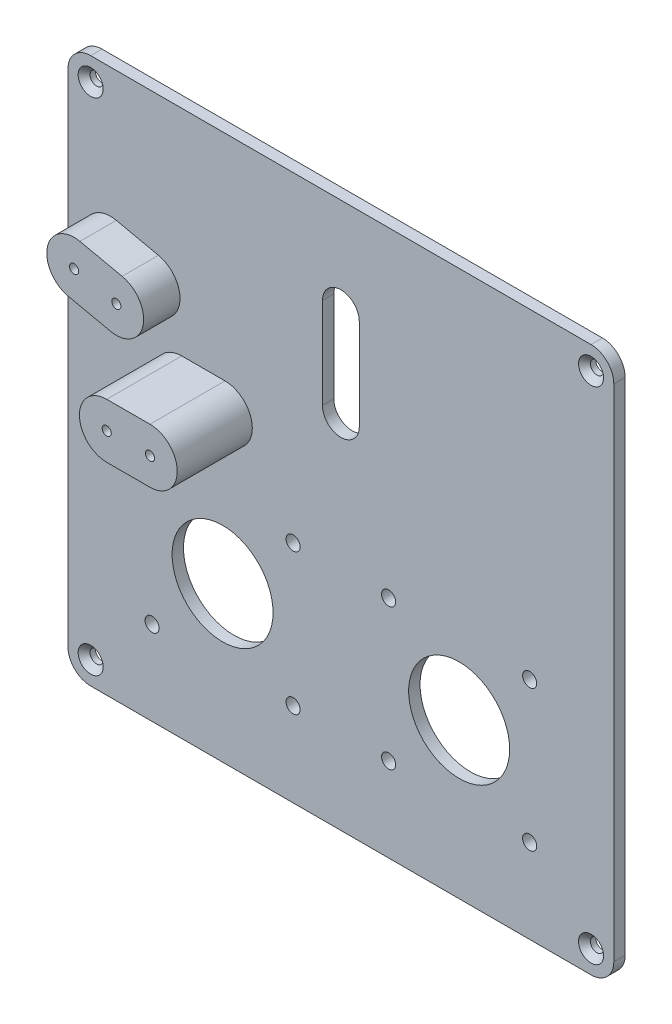
SolidWorks part; units mm, degrees
ref_plane "Front Plane" through (0, 0, 0) normal (0, 0, 1) x (1, 0, 0)
ref_plane "Top Plane" through (0, 0, 0) normal (0, 1, 0) x (1, 0, 0)
ref_plane "Right Plane" through (0, 0, 0) normal (1, 0, 0) x (0, 0, -1)
sketch "Sketch1" plane through (0, 0, 0) normal (0, 0, 1) x (1, 0, 0)
  line L1 (86, -34) -> (-34, -34)
  line L2 (86, -34) -> (86, 86)
  line L3 (86, 86) -> (-34, 86)
  line L4 (-34, -34) -> (-34, 86)
  line L6 (73, 0) -> (86, 0) construction
  line L7 (73, -17) -> (73, 17) construction
  line L8 (-21, 0) -> (-34, 0) construction
  line L9 (-21, 17) -> (-21, -17) construction
  line L10 (35, -21) -> (69, -21) construction
  line L11 (52, 0) -> (0, 0) construction
  line L12 (26, 0) -> (26, 54.8845) construction
  line L13 (53.4457, 56.6124) -> (56.9901, 0.3142)
  line L14 (7.2779, 34.7417) -> (48.596, -3.6623)
  circle A0 centre (0, 0) radius 11 construction
  circle A1 centre (52, 0) radius 11 construction
  circle A2 centre (0, 0) radius 11
  circle A3 centre (52, 0) radius 11
  circle A7 centre (36.5, 15.5) radius 1.5 construction
  circle A14 centre (-15.5, -15.5) radius 1.5 construction
  circle A15 centre (-15.5, 15.5) radius 1.5 construction
  circle A16 centre (15.5, 15.5) radius 1.5 construction
  circle A17 centre (15.5, -15.5) radius 1.5 construction
  circle A18 centre (36.5, -15.5) radius 1.5 construction
  circle A19 centre (67.5, 15.5) radius 1.5 construction
  circle A20 centre (67.5, -15.5) radius 1.5 construction
  circle A21 centre (-15.5, -15.5) radius 1.5
  circle A22 centre (-15.5, 15.5) radius 1.5
  circle A23 centre (15.5, 15.5) radius 1.5
  circle A24 centre (15.5, -15.5) radius 1.5
  circle A25 centre (36.5, 15.5) radius 1.5
  circle A26 centre (36.5, -15.5) radius 1.5
  circle A27 centre (67.5, 15.5) radius 1.5
  circle A28 centre (67.5, -15.5) radius 1.5
  arc A29 (53.4457, 56.6124) -> (7.2779, 34.7417) centre (26, 54.8845) ccw
  arc A30 (48.596, -3.6623) -> (56.9901, 0.3142) centre (52, 0) ccw
  circle A31 centre (0, 0) radius 5
  circle A32 centre (26, 54.8845) radius 4
  dimension "D4" = 27.5
  dimension "D5" = 10
  dimension "D6" = 232
  dimension "D7" = 8
  dimension "D1" = 120
  dimension "D2" = 120
  dimension "D3" = 13
sketch "Sketch4" plane through (0, 0, 0) normal (0, 0, 1) x (1, 0, 0)
  line L0 (26, 64.8845) -> (26, 44.8845) construction
  line L1 (26, 0) -> (26, 54.8845) construction
  line L2 (30.05, 64.8845) -> (30.05, 44.8845)
  line L3 (21.95, 64.8845) -> (21.95, 44.8845)
  line L4 (86, -34) -> (86, 86) construction
  line L5 (86, 86) -> (-34, 86) construction
  line L6 (-34, -34) -> (-34, 86) construction
  line L7 (86, -34) -> (-34, -34) construction
  line L8 (86, -34) -> (86, 86)
  line L9 (86, 86) -> (-34, 86)
  line L10 (-34, -34) -> (-34, 86)
  line L11 (86, -34) -> (-34, -34)
  arc A0 (30.05, 64.8845) -> (21.95, 64.8845) centre (26, 64.8845) ccw
  arc A1 (21.95, 44.8845) -> (30.05, 44.8845) centre (26, 44.8845) ccw
  point P5 (26, 54.8845)
  point P12 (67.5, -15.5)
  point P15 (36.5, -15.5)
  point P17 (36.5, 15.5)
  point P19 (67.5, 15.5)
  point P21 (15.5, 15.5)
  point P23 (-15.5, 15.5)
  point P25 (-15.5, -15.5)
  point P27 (15.5, -15.5)
  point P29 (52, 0)
  point P31 (0, 0)
  dimension "D2" = 4.05
  dimension "D1" = 20
extrude "Boss-Extrude2" add sketch "Sketch4" along normal blind 2.5
fillet "Fillet1" radius 5 4 edges at (86, 86, 1.25) (-34, 86, 1.25) (-34, -34, 1.25) (86, -34, 1.25)
sketch "Sketch5" plane through (0, 0, 0) normal (0, 0, -1) x (-1, 0, 0)
  line L4 (29, 86) -> (-81, 86)
  line L5 (-86, 81) -> (-86, -29)
  line L6 (-81, -34) -> (29, -34)
  line L7 (34, -29) -> (34, 81)
  line L8 (29, 86) -> (-81, 86)
  line L9 (-86, 81) -> (-86, -29)
  line L10 (-81, -34) -> (29, -34)
  line L11 (34, -29) -> (34, 81)
  arc A4 (-81, 86) -> (-86, 81) centre (-81, 81) ccw
  arc A5 (-86, -29) -> (-81, -34) centre (-81, -29) ccw
  arc A6 (29, -34) -> (34, -29) centre (29, -29) ccw
  arc A7 (34, 81) -> (29, 86) centre (29, 81) ccw
  arc A8 (-81, 86) -> (-86, 81) centre (-81, 81) ccw
  arc A9 (-86, -29) -> (-81, -34) centre (-81, -29) ccw
  arc A10 (29, -34) -> (34, -29) centre (29, -29) ccw
  arc A11 (34, 81) -> (29, 86) centre (29, 81) ccw
  dimension "D1" = 0
hole_wizard "Ø3.1 (3.1) Diameter Hole1" positions "Sketch6" profile "Sketch7" hole size "Ø3.1" standard "ANSI Metric" end condition through all
sketch "Sketch6" plane through (0, 0, 2.5) normal (0, 0, 1) x (1, 0, 0)
  point P0 (-15.5, -15.5)
  point P3 (-15.5, 15.5)
  point P6 (15.5, 15.5)
  point P9 (15.5, -15.5)
  point P12 (36.5, -15.5)
  point P15 (36.5, 15.5)
  point P18 (67.5, -15.5)
  point P21 (67.5, 15.5)
sketch "Sketch7" plane through (-15.5, -15.5, 2.5) normal (1, 0, 0) x (0, -1, 0)
  line L0 (0, 0) -> (0, 2.5)
  line L1 (0, 2.5) -> (1.55, 2.5)
  line L2 (1.55, 2.5) -> (1.55, 0)
  line L5 (1.55, 0) -> (0, 0)
  line L11 (0, -6.35) -> (0, 107.95) construction
  dimension "Thru Hole Dia." = 3.1
  dimension "Thru Hole Depth" = 2.5
sketch "Sketch8" plane through (0, 0, 2.5) normal (0, 0, 1) x (1, 0, 0)
  circle A5 centre (0, 0) radius 11.1
  circle A6 centre (0, 0) radius 11.1
  circle A8 centre (52, 0) radius 11.1
  circle A9 centre (52, 0) radius 11.1
  dimension "D1" = 0.1
  dimension "D2" = 0.1
extrude "Cut-Extrude1" cut sketch "Sketch8" against normal blind 10
sketch "Sketch9" plane through (0, 0, 2.5) normal (0, 0, 1) x (1, 0, 0)
  line L0 (26, 44.8845) -> (26, 64.8845) construction
  line L1 (21.9, 44.8845) -> (21.9, 64.8845)
  line L2 (30.1, 44.8845) -> (30.1, 64.8845)
  arc A0 (21.9, 44.8845) -> (30.1, 44.8845) centre (26, 44.8845) ccw
  arc A1 (30.1, 64.8845) -> (21.9, 64.8845) centre (26, 64.8845) ccw
  point P2 (26, 54.8845)
  dimension "D1" = 4.1
sketch "Sketch10" plane through (0, 0, 2.5) normal (0, 0, 1) x (1, 0, 0)
  line L0 (-8.9685, 32.85) -> (0.5315, 32.85) construction
  line L1 (-8.9685, 38.85) -> (0.5315, 38.85)
  line L2 (-8.9685, 26.85) -> (0.5315, 26.85)
  arc A0 (-8.9685, 38.85) -> (-8.9685, 26.85) centre (-8.9685, 32.85) ccw
  arc A1 (0.5315, 26.85) -> (0.5315, 38.85) centre (0.5315, 32.85) ccw
  circle A2 centre (0.5315, 32.85) radius 1
  circle A3 centre (-8.9685, 32.85) radius 1
  point P2 (-4.2185, 32.85)
  dimension "D1" = 9.5
  dimension "D2" = 2
  dimension "D3" = 2
  dimension "D4" = 6
extrude "Boss-Extrude3" add sketch "Sketch10" along normal up to surface (16.5 mm away)
sketch "Sketch11" plane through (0, 0, 2.5) normal (0, 0, 1) x (1, 0, 0)
  line L0 (-24.6419, 51.5981) -> (-15.3581, 49.5828) construction
  line L1 (-23.3691, 57.4616) -> (-14.0853, 55.4463)
  line L2 (-25.9147, 45.7347) -> (-16.6309, 43.7194)
  line L3 (-34, 81) -> (-34, -29) construction
  line L4 (81, 86) -> (-29, 86) construction
  arc A0 (-23.3691, 57.4616) -> (-25.9147, 45.7347) centre (-24.6419, 51.5981) ccw
  arc A1 (-16.6309, 43.7194) -> (-14.0853, 55.4463) centre (-15.3581, 49.5828) ccw
  circle A2 centre (-15.3581, 49.5828) radius 1
  circle A3 centre (-24.6419, 51.5981) radius 1
  point P2 (-20, 50.5905)
  dimension "D2" = 6
  dimension "D5" = 2
  dimension "D6" = 2
  dimension "D7" = 35.4095
  dimension "D1" = 9.5
  dimension "D3" = 14
  dimension "D4" = 77.752
extrude "Boss-Extrude4" add sketch "Sketch11" along normal blind 8
hole_wizard "CSK for M2.5 Flat Head Machine Screw2" positions "Sketch13" profile "Sketch14" countersink size "M2.5" standard "ANSI Metric" end condition through all
sketch "Sketch13" plane through (0, 0, 2.5) normal (0, 0, 1) x (1, 0, 0)
  point P2 (81, 81)
  point P5 (81, -29)
  point P8 (-29, -29)
  point P11 (-29, 81)
sketch "Sketch14" plane through (81, 81, 2.5) normal (1, 0, 0) x (0, -1, 0)
  line L0 (0, 0) -> (0, 2.5)
  line L1 (0, 2.5) -> (1.45, 2.5)
  line L2 (1.45, 2.5) -> (1.45, 1.3)
  line L3 (1.45, 1.3) -> (2.75, 0)
  line L5 (2.75, 0) -> (0, 0)
  line L6 (-1.45, 1.3) -> (-2.75, 0) construction
  line L11 (0, -6.35) -> (0, 107.95) construction
  dimension "Thru Hole Dia." = 2.9
  dimension "Thru Hole Depth" = 2.5
  dimension "Near C'Sink Dia." = 5.5
  dimension "Near C'Sink Angle" = 90
